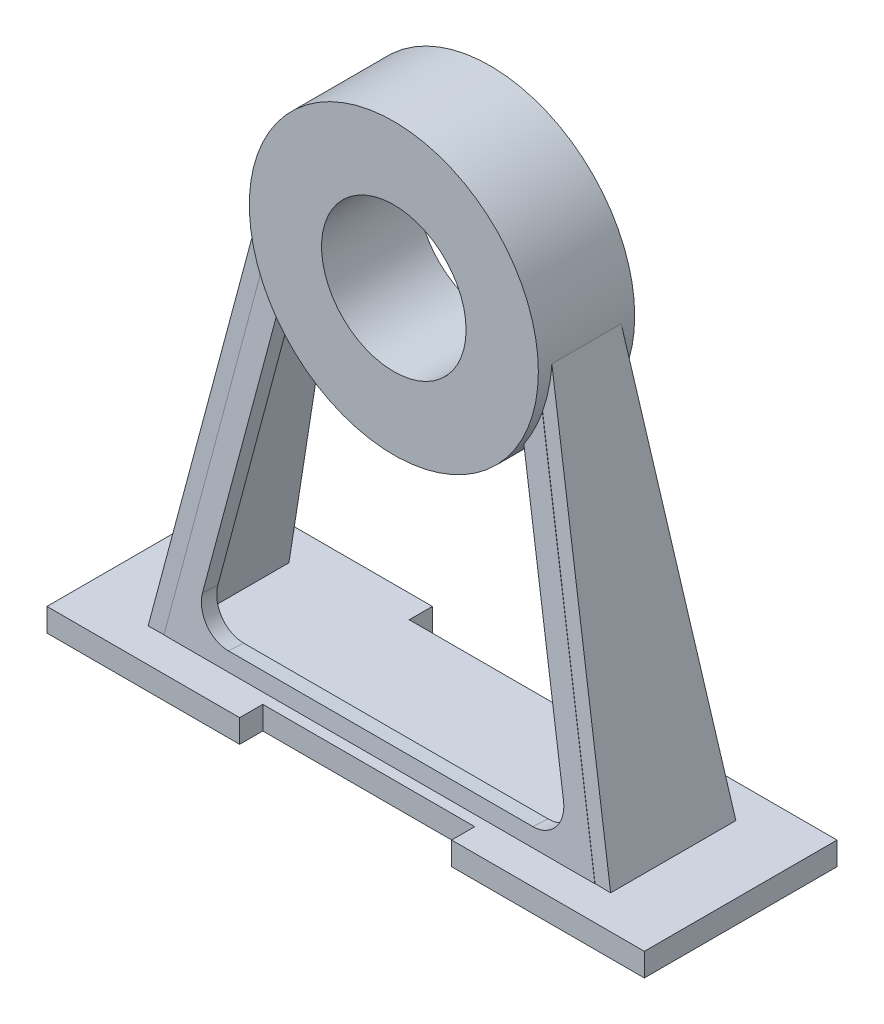
SolidWorks part; units mm, degrees
material "AISI 1020"
ref_plane "Front Plane" through (0, 0, 0) normal (0, 0, 1) x (1, 0, 0)
ref_plane "Top Plane" through (0, 0, 0) normal (0, 1, 0) x (1, 0, 0)
ref_plane "Right Plane" through (0, 0, 0) normal (1, 0, 0) x (0, 0, -1)
sketch "Sketch1" plane through (0, 0, 0) normal (0, 1, 0) x (1, 0, 0)
  line L0 (0, -50) -> (0, 50)
  line L1 (0, 50) -> (100, 50)
  line L2 (100, 50) -> (100, 38)
  line L3 (100, 38) -> (210, 38)
  line L4 (210, 38) -> (210, 50)
  line L5 (210, 50) -> (310, 50)
  line L6 (0, 0) -> (366.3604, 0) construction
  line L7 (210, -38) -> (210, -50)
  line L8 (210, -50) -> (310, -50)
  line L9 (0, -50) -> (100, -50)
  line L10 (100, -38) -> (210, -38)
  line L11 (100, -50) -> (100, -38)
  line L12 (310, 50) -> (310, -50)
  dimension "D1" = 50
  dimension "D2" = 100
  dimension "D3" = 110
  dimension "D4" = 100
  dimension "D5" = 12
extrude "Boss-Extrude1" add sketch "Sketch1" along normal blind 12
sketch "Sketch2" plane through (0, 0, 0) normal (0, 0, 1) x (1, 0, 0)
  line L0 (155, 0) -> (155, 220) construction
  line L1 (100, 0) -> (210, 0) construction
  circle A0 centre (155, 220) radius 75
  circle A1 centre (155, 220) radius 37.5
  dimension "D1" = 75
  dimension "D2" = 150
  dimension "D3" = 220
extrude "Boss-Extrude2" add sketch "Sketch2" along normal mid plane 50 separate body
sketch "Sketch3" plane through (0, 12, 0) normal (0, 1, 0) x (1, 0, 0)
  line L0 (35, 32.5) -> (35, -32.5)
  line L1 (0, 50) -> (0, -50) construction
  point P0 (0, 0)
  point P3 (35, 0)
  dimension "D1" = 65
  dimension "D2" = 35
ref_plane "Plane1" through (80, 0, 0) normal (-1, 0, 0) x (0, 0, 1)
sketch "Sketch4" plane through (80, 0, 0) normal (-1, 0, 0) x (0, 0, 1)
  line L0 (-18, 220) -> (18, 220)
  point P3 (0, 220)
  dimension "D1" = 36
  dimension "D2" = 220
ref_plane "Plane2" through (30.955, -6.697, 0) normal (0.9774, -0.2115, 0) x (0, 0, -1)
sketch "Sketch6" plane through (30.955, -6.697, 0) normal (0.9774, -0.2115, 0) x (0, 0, -1)
  line L0 (18, 231.9417) -> (-18, 231.9417) construction
  line L1 (18, 231.9417) -> (-18, 231.9417)
  line L2 (32.5, 19.1295) -> (-32.5, 19.1295) construction
  line L3 (32.5, 19.1295) -> (-32.5, 19.1295)
  line L4 (-18, 231.9417) -> (-32.5, 19.1295)
  line L5 (18, 231.9417) -> (32.5, 19.1295)
extrude "Boss-Extrude3" add sketch "Sketch6" along normal blind 8
ref_plane "Plane3" through (155, 0, 0) normal (1, 0, 0) x (0, 0, -1)
mirror "Mirror2" about plane through (155, 0, 0) normal (1, 0, 0) of "Boss-Extrude3"
ref_plane "Plane4" through (0, 2.3127, 33.1753) normal (0, -0.0695, -0.9976) x (-1, 0, 0)
sketch "Sketch7" plane through (0, 2.3127, 33.1753) normal (0, -0.0695, -0.9976) x (-1, 0, 0)
  line L0 (-83.3734, 195.9294) -> (-43.1851, 9.719) construction
  line L1 (-83.3242, 195.7011) -> (-43.1851, 9.719)
  line L2 (-226.6266, 195.9294) -> (-266.8149, 9.719) construction
  line L3 (-226.6758, 195.7011) -> (-266.8149, 9.719)
  line L4 (-91.6955, 177.6076) -> (-61.3241, 36.8835)
  line L5 (-218.3045, 177.6076) -> (-248.6759, 36.8835)
  line L6 (-75.9865, 18.719) -> (-234.0135, 18.719)
  line L8 (-95.1034, 193.3978) -> (-54.915, 7.1874) construction
  line L9 (-214.8966, 193.3978) -> (-255.085, 7.1874) construction
  line L10 (-226.6266, 195.9294) -> (-266.8149, 9.719) construction
  line L11 (-83.3734, 195.9294) -> (-43.1851, 9.719) construction
  line L12 (-43.1851, 9.719) -> (-266.8149, 9.719)
  arc A0 (-234.0135, 18.719) -> (-248.6759, 36.8835) centre (-234.0135, 33.719) cw
  arc A1 (-75.9865, 18.719) -> (-61.3241, 36.8835) centre (-75.9865, 33.719) ccw
  ellipse E0 centre (-155, 217.7288) end of major axis (-80, 217.7288) minor radius 74.8184 construction
  ellipse E1 centre (-155, 217.7288) end of major axis (-230, 217.7288) minor radius 74.8184 (-226.6758, 195.7011) -> (-218.3045, 177.6076) ccw
  ellipse E2 centre (-155, 217.7288) end of major axis (-80, 217.7288) minor radius 74.8184 (-91.6955, 177.6076) -> (-83.3242, 195.7011) ccw
  dimension "D4" = 15
  dimension "D3" = 9
  dimension "D1" = 12
  dimension "D2" = 12
extrude "Boss-Extrude11" add sketch "Sketch7" along normal blind 8 separate body
